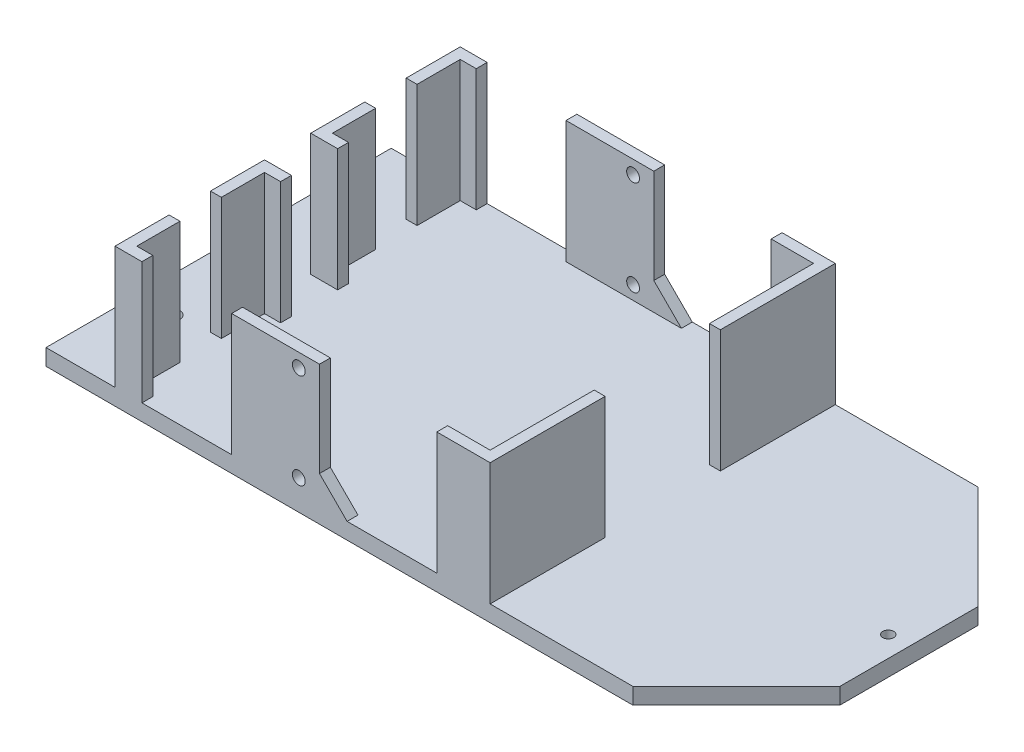
SolidWorks part; units mm, degrees
ref_plane "Front Plane" through (0, 0, 0) normal (0, 0, 1) x (1, 0, 0)
ref_plane "Top Plane" through (0, 0, 0) normal (0, 1, 0) x (1, 0, 0)
ref_plane "Right Plane" through (0, 0, 0) normal (1, 0, 0) x (0, 0, -1)
sketch "Sketch1" plane through (0, 0, 0) normal (0, 1, 0) x (1, 0, 0)
  line L1 (-63.5, 31.75) -> (63.5, 31.75)
  line L2 (-63.5, 31.75) -> (-63.5, -31.75)
  line L3 (-63.5, -31.75) -> (63.5, -31.75)
  line L4 (63.5, 31.75) -> (63.5, -31.75)
  line L5 (-63.5, 31.75) -> (63.5, -31.75) construction
  line L6 (-63.5, -31.75) -> (63.5, 31.75) construction
  point P0 (0, 0)
  dimension "D1" = 63.5
  dimension "D2" = 127
extrude "Boss-Extrude1" add sketch "Sketch1" along normal blind 3
sketch "Sketch2" plane through (0, 3, 0) normal (0, 1, 0) x (1, 0, 0)
  line L0 (-61.5, 29.75) -> (-63.5, 29.75)
  line L1 (-63.5, 31.75) -> (63.5, 31.75)
  line L2 (-63.5, 31.75) -> (-63.5, -31.75)
  line L3 (-63.5, -31.75) -> (63.5, -31.75)
  line L4 (63.5, 31.75) -> (63.5, -31.75)
  line L5 (-63.5, 31.75) -> (63.5, -31.75) construction
  line L6 (-63.5, -31.75) -> (63.5, 31.75) construction
  line L7 (-61.5, 29.75) -> (61.5, 29.75)
  line L8 (-61.5, 29.75) -> (-61.5, -29.75)
  line L9 (-61.5, -29.75) -> (61.5, -29.75)
  line L10 (61.5, 29.75) -> (61.5, -29.75)
  line L11 (-61.5, 29.75) -> (61.5, -29.75) construction
  line L12 (-61.5, -29.75) -> (61.5, 29.75) construction
  line L13 (-61.5, -29.75) -> (-63.5, -29.75)
  point P0 (0, 0)
  point P7 (0, 0)
  line M5 (63.5, -31.75) -> (63.5, 31.75)
  line M6 (63.5, 31.75) -> (-63.5, 31.75)
  line M7 (-63.5, 31.75) -> (-63.5, -31.75)
  line M8 (-63.5, -31.75) -> (63.5, -31.75)
  dimension "D1" = 2
  dimension "D2" = 2
extrude "Boss-Extrude2" add sketch "Sketch2" along normal blind 22.5 contours L9 L13 L2 L0 L7 L10 M8 M5 M6 M7
sketch "Sketch3" plane through (61.5, 0, 0) normal (-1, 0, 0) x (0, 0, 1)
  line L0 (29.75, 3) -> (-29.75, 3) construction
  line L1 (-7.62, 25.5) -> (7.62, 25.5)
  line L2 (-7.62, 25.5) -> (-7.62, 3)
  line L3 (-7.62, 3) -> (7.62, 3)
  line L4 (7.62, 25.5) -> (7.62, 3)
  line L5 (-7.62, 25.5) -> (7.62, 3) construction
  line L6 (-7.62, 3) -> (7.62, 25.5) construction
  line L8 (0, -55) -> (0, 55) construction
  line L9 (-29.75, 25.5) -> (29.75, 25.5) construction
  point P0 (0, 14.25)
  dimension "D1" = 7.62
extrude "Cut-Extrude1" cut sketch "Sketch3" against normal through all
sketch "Sketch4" plane through (0, 3, 0) normal (0, 1, 0) x (1, 0, 0)
  line L0 (-63.5, -29.75) -> (61.5, -29.75) construction
  line L1 (-48.8, -29.75) -> (16.2, -29.75)
  line L2 (-48.8, -29.75) -> (-48.8, -6.25)
  line L3 (-48.8, -6.25) -> (16.2, -6.25)
  line L4 (16.2, -29.75) -> (16.2, -6.25)
  line L5 (-50.8, -4.25) -> (18.2, -4.25)
  line L6 (18.2, -31.75) -> (18.2, -4.25)
  line L7 (-50.8, -31.75) -> (18.2, -31.75)
  line L8 (-50.8, -31.75) -> (-50.8, -4.25)
  line L9 (-55, 0) -> (55, 0) construction
  line L10 (-50.8, 31.75) -> (-50.8, 4.25)
  line L11 (-50.8, 31.75) -> (18.2, 31.75)
  line L12 (18.2, 31.75) -> (18.2, 4.25)
  line L13 (-50.8, 4.25) -> (18.2, 4.25)
  line L14 (16.2, 29.75) -> (16.2, 6.25)
  line L15 (-48.8, 6.25) -> (16.2, 6.25)
  line L16 (-48.8, 29.75) -> (-48.8, 6.25)
  line L17 (-48.8, 29.75) -> (16.2, 29.75)
  line L18 (-63.5, 29.75) -> (-63.5, -29.75) construction
  line L19 (5.5, -4.25) -> (5.5, -6.25)
  line L20 (-50.8, -14.19) -> (-48.8, -14.19)
  line L21 (-50.8, -21.81) -> (-48.8, -21.81)
  line L22 (-49.8, -14.19) -> (-49.8, -21.81) construction
  line L23 (-50.8, 21.81) -> (-48.8, 21.81)
  line L24 (-50.8, 14.19) -> (-48.8, 14.19)
  line L25 (16.2, -10.6) -> (18.2, -10.6)
  line L26 (5.5, 4.25) -> (5.5, 6.25)
  line L27 (16.2, 10.6) -> (18.2, 10.6)
  point P31 (-49.8, -18)
  point P32 (-48.8, -18)
  line M3 (-63.5, -29.75) -> (61.5, -29.75)
  line M9 (61.5, 29.75) -> (-63.5, 29.75)
  dimension "D1" = 23.5
  dimension "D2" = 65
  dimension "D3" = 12.7
  dimension "D5" = 7.62
  dimension "D6" = 12.7
  dimension "D7" = 6.35
  dimension "D4" = 2
extrude "Boss-Extrude4" add sketch "Sketch4" along normal up to surface (22.5 mm away) contours L24 L10 L13 L12 L14 L15 L16 M9 | L10 L23 L16 M9 | L21 L8 L2 M3 | L8 L20 L2 L3 L4 L6 L5 M3 | L25 L4 L6 M3 | L14 L27 L12 M9 up to face at (20.5, 25.5, -23.04)
sketch "Sketch5" plane through (0, 0, 29.75) normal (0, 0, -1) x (-1, 0, 0)
  line L1 (29.345, 25.5) -> (45.855, 25.5)
  line L2 (29.345, 25.5) -> (29.345, 3)
  line L3 (29.345, 3) -> (45.855, 3)
  line L4 (45.855, 25.5) -> (45.855, 3)
  line L5 (29.345, 25.5) -> (45.855, 3) construction
  line L6 (29.345, 3) -> (45.855, 25.5) construction
  line L9 (48.8, 3) -> (-16.2, 3) construction
  line L10 (63.5, 25.5) -> (-63.5, 25.5) construction
  point P0 (37.6, 14.25)
  dimension "D1" = 11.2
  dimension "D2" = 16.51
extrude "Cut-Extrude2" cut sketch "Sketch5" against normal through all and the other way through all
sketch "Sketch6" plane through (0, 25.5, 0) normal (0, 1, 0) x (1, 0, 0)
  line L0 (18.2, 29.75) -> (18.2, 31.75)
  line L1 (63.5, 31.75) -> (-29.345, 31.75) construction
  line L2 (18.2, -29.75) -> (18.2, -31.75)
  line L3 (-29.345, -31.75) -> (63.5, -31.75) construction
  line L4 (18.2, -31.75) -> (63.5, -31.75)
  line L5 (63.5, -31.75) -> (63.5, -7.62)
  line L6 (63.5, -7.62) -> (61.5, -7.62)
  line L7 (61.5, -7.62) -> (61.5, -29.75)
  line L8 (61.5, -29.75) -> (18.2, -29.75)
  line L9 (18.2, 31.75) -> (63.5, 31.75)
  line L10 (63.5, 31.75) -> (63.5, 7.62)
  line L11 (63.5, 7.62) -> (61.5, 7.62)
  line L12 (61.5, 7.62) -> (61.5, 29.75)
  line L13 (61.5, 29.75) -> (18.2, 29.75)
  line L14 (-63.5, 31.75) -> (-63.5, 29.75)
  line L15 (-63.5, 29.75) -> (-50.8, 29.75)
  line L16 (-50.8, 29.75) -> (-50.8, 31.75)
  line L17 (-45.855, 31.75) -> (-63.5, 31.75) construction
  line L18 (-50.8, 31.75) -> (-63.5, 31.75)
  line L19 (-63.5, -29.75) -> (-63.5, -31.75)
  line L20 (-63.5, -29.75) -> (-50.8, -29.75)
  line L22 (-50.8, -29.75) -> (-50.8, -31.75)
  line L23 (-63.5, -31.75) -> (-45.855, -31.75) construction
  line L24 (-50.8, -31.75) -> (-63.5, -31.75)
extrude "Cut-Extrude3" cut sketch "Sketch6" against normal up to surface (22.5 mm away) up to face at (-48.485, 3, -8.23)
sketch "Sketch8" plane through (0, 0, 31.75) normal (0, 0, 1) x (1, 0, 0)
  line L0 (-29.345, 3) -> (18.2, 3)
  line L1 (-17, 3) -> (-17, 25.5) construction
  line L2 (-29.345, 25.5) -> (18.2, 25.5) construction
  line L3 (-48.8, 3) -> (-48.8, 25.5) construction
  circle A0 centre (-17, 23) radius 1.1811
  circle A1 centre (-17, 5.5) radius 1.1811
  point P10 (-17, 5.5)
  point P11 (-17, 23)
  dimension "D4" = 2.3622
  dimension "D1" = 31.8
  dimension "D2" = 17.5
  dimension "D3" = 2.5
extrude "Cut-Extrude4" cut sketch "Sketch8" against normal through all contours A0 L1 | L1 A0 | A1 L1 | L1 A1
sketch "Sketch10" plane through (0, 0, 0) normal (0, -1, 0) x (1, 0, 0)
  line L0 (44.45, 31.75) -> (63.5, 12.7)
  line L1 (-63.5, 31.75) -> (63.5, 31.75) construction
  line L2 (63.5, 31.75) -> (63.5, -31.75) construction
  line L3 (63.5, 12.7) -> (63.5, -12.7)
  line L4 (63.5, -12.7) -> (44.45, -31.75)
  line L5 (63.5, -31.75) -> (-63.5, -31.75) construction
  line L6 (14.025, 0) -> (-14.025, 0) construction
  line L9 (44.45, 31.75) -> (63.5, 31.75)
  line L10 (63.5, 31.75) -> (63.5, 12.7)
  line L11 (63.5, -12.7) -> (63.5, -31.75)
  line L12 (63.5, -31.75) -> (44.45, -31.75)
  point P6 (63.5, 0)
  point P17 (59.69, 0)
  line M3 (63.5, -31.75) -> (63.5, 31.75)
  line M4 (63.5, 31.75) -> (-63.5, 31.75)
  line M6 (-63.5, -31.75) -> (63.5, -31.75)
  dimension "D1" = 25.4
  dimension "D2" = 3.81
  dimension "D3" = 45
  dimension "D4" = 45
extrude "Cut-Extrude5" cut sketch "Sketch10" against normal through all contours L0 M4 M3 | L4 M3 M6
hole_wizard "Ø2.0mm Dowel Hole1" positions "3DSketch1" profile "Sketch12" hole size "Ø2.0" standard "ANSI Metric" end condition through all
sketch3d "3DSketch1"
  point P2 (59.69, 0, 0)
sketch "Sketch12" plane through (59.69, 0, 0) normal (1, 0, 0) x (0, 0, -1)
  line L0 (0, 0) -> (0, 25.5)
  line L1 (0, 25.5) -> (1, 25.5)
  line L2 (1, 25.5) -> (1, 0)
  line L5 (1, 0) -> (0, 0)
  line L11 (0, -6.35) -> (0, 107.95) construction
  dimension "Thru Hole Dia." = 2
  dimension "Thru Hole Depth" = 25.5
sketch "Sketch13" plane through (0, 0, 6.25) normal (0, 0, 1) x (1, 0, 0)
  line L0 (-29.345, 25.5) -> (-29.345, 3)
  line L1 (-29.345, 25.5) -> (5.5, 25.5)
  line L2 (5.5, 25.5) -> (5.5, 3)
  line L3 (5.5, 3) -> (-29.345, 3)
extrude "Cut-Extrude6" cut sketch "Sketch13" against normal up to surface (12.5 mm away) up to face at (-18.1811, 23, -6.25)
sketch "Sketch14" plane through (0, 3, 0) normal (0, 1, 0) x (1, 0, 0)
  line L0 (-63.5, 31.75) -> (-63.5, -31.75) construction
  line L1 (-63.5, 15) -> (-57.15, 15)
  line L2 (-63.5, 15) -> (-63.5, -15)
  line L3 (-63.5, -15) -> (-57.15, -15)
  line L4 (-57.15, 15) -> (-57.15, -15)
  line L5 (-14.025, 0) -> (14.025, 0) construction
  point P6 (-57.15, 0)
  dimension "D1" = 30
  dimension "D2" = 6.35
hole_wizard "Ø3.0mm Dowel Hole1" positions "3DSketch2" profile "Sketch15" hole size "Ø3.0" standard "ANSI Metric" end condition through all
sketch3d "3DSketch2"
  point P0 (-57.15, 3, -15)
  point P3 (-57.15, 3, 15)
sketch "Sketch15" plane through (-57.15, 3, -15) normal (1, 0, 0) x (0, 0, 1)
  line L0 (0, 0) -> (0, 3)
  line L1 (0, 3) -> (1.5, 3)
  line L2 (1.5, 3) -> (1.5, 0)
  line L5 (1.5, 0) -> (0, 0)
  line L11 (0, -6.35) -> (0, 107.95) construction
  dimension "Thru Hole Dia." = 3
  dimension "Thru Hole Depth" = 3
sketch "Sketch16" plane through (0, 0, 31.75) normal (0, 0, 1) x (1, 0, 0)
  line L0 (-29.345, 25.5) -> (18.2, 25.5) construction
  line L1 (-13.19, 25.5) -> (8.4, 25.5)
  line L2 (-13.19, 25.5) -> (-13.19, 3)
  line L3 (-13.19, 3) -> (8.4, 3)
  line L4 (8.4, 25.5) -> (8.4, 3)
  line L5 (44.45, 3) -> (18.2, 3) construction
  line L6 (-13.19, 8.08) -> (-8.11, 3)
  circle A0 centre (-17, 23) radius 1.1811 construction
  line M9 (18.2, 25.5) -> (-29.345, 25.5)
  dimension "D1" = 3.81
  dimension "D2" = 21.59
  dimension "D3" = 45
  dimension "D4" = 5.08
extrude "Cut-Extrude7" cut sketch "Sketch16" against normal through all contours L2 L6 L3 L4 M9
